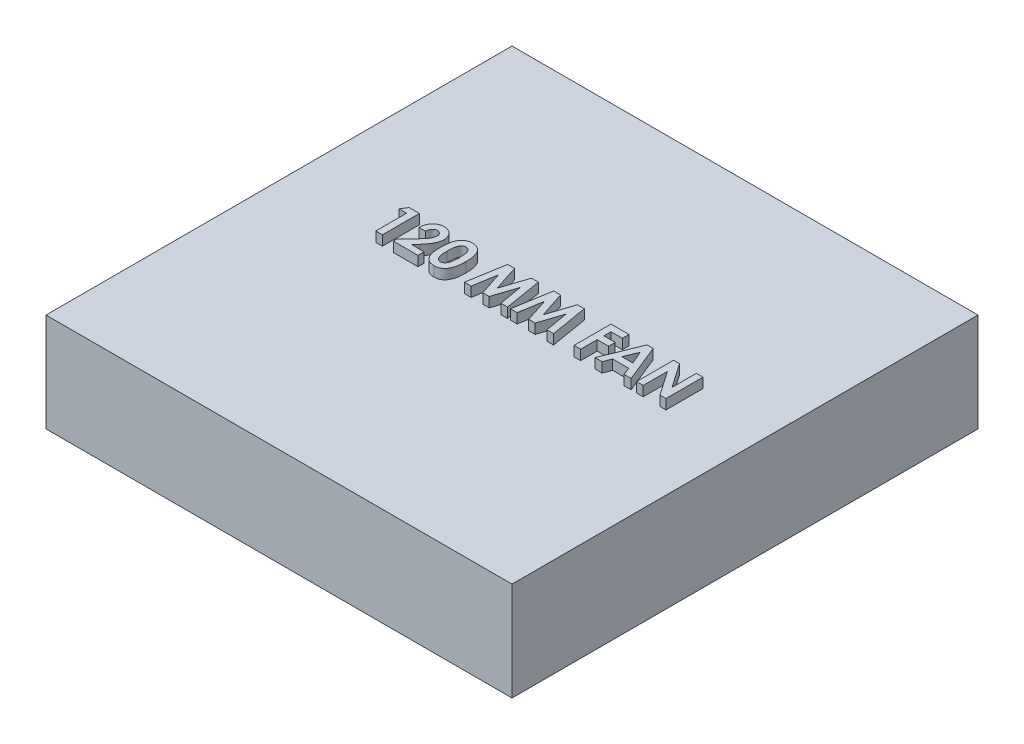
SolidWorks part; units mm, degrees
ref_plane "Front Plane" through (0, 0, 0) normal (0, 0, 1) x (1, 0, 0)
ref_plane "Top Plane" through (0, 0, 0) normal (0, 1, 0) x (1, 0, 0)
ref_plane "Right Plane" through (0, 0, 0) normal (1, 0, 0) x (0, 0, -1)
sketch "Sketch1" plane through (0, 0, 0) normal (0, 1, 0) x (1, 0, 0)
  line L1 (-60, -60) -> (60, -60)
  line L2 (-60, -60) -> (-60, 60)
  line L3 (-60, 60) -> (60, 60)
  line L4 (60, -60) -> (60, 60)
  line L5 (-60, -60) -> (60, 60) construction
  line L6 (-60, 60) -> (60, -60) construction
  point P0 (0, 0)
  dimension "D1" = 120
extrude "Boss-Extrude1" add sketch "Sketch1" along normal blind 25.4
sketch "Sketch2" plane through (0, 25.4, 0) normal (0, 1, 0) x (1, 0, 0)
  text T0 "<b>120 MM FAN</b>" font "Century Gothic" height in points 36
extrude "Boss-Extrude2" add sketch "Sketch2" along normal blind 2.54
